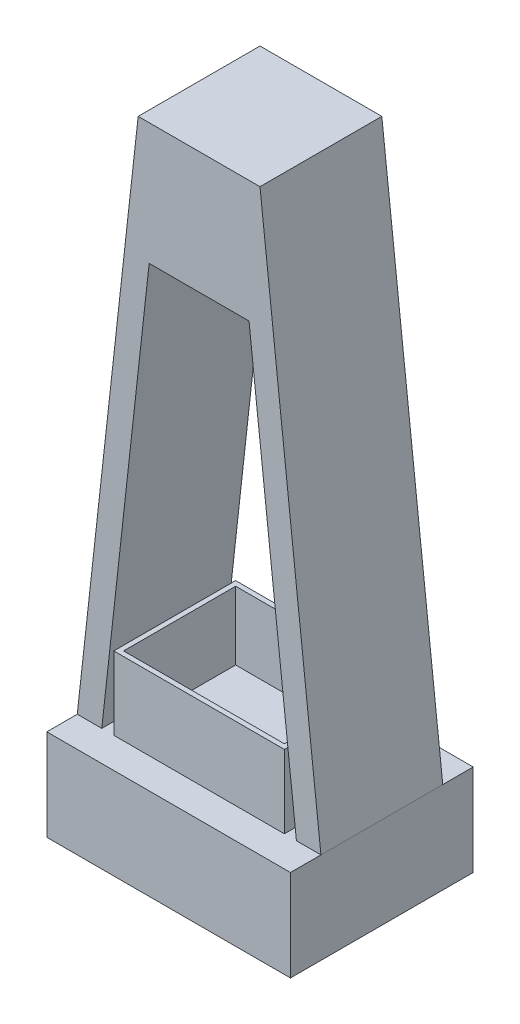
SolidWorks part; units mm, degrees
ref_plane "Front Plane" through (0, 0, 0) normal (0, 0, 1) x (1, 0, 0)
ref_plane "Top Plane" through (0, 0, 0) normal (0, 1, 0) x (1, 0, 0)
ref_plane "Right Plane" through (0, 0, 0) normal (1, 0, 0) x (0, 0, -1)
sketch "Sketch2" plane through (0, 0, 0) normal (0, 0, 1) x (1, 0, 0)
  line L0 (-50, 225) -> (50, 225)
  line L1 (50, 225) -> (100, -225)
  line L2 (100, -225) -> (-100, -225)
  line L3 (-100, -225) -> (-50, 225)
  point P3 (-48.9615, 146.9013)
  point P5 (0, 225)
  point P6 (0, -225)
  point P7 (-64.057, 145.9255)
  point P8 (-75, 0)
  dimension "D1" = 450
  dimension "D2" = 200
  dimension "D3" = 100
extrude "Boss-Extrude1" add sketch "Sketch2" along normal blind 100
sketch "Sketch3" plane through (0, -225, 0) normal (0, -1, 0) x (1, 0, 0)
  line L0 (-100, 100) -> (-100, 0) construction
  line L1 (-100, -25) -> (100, -25)
  line L2 (-100, -25) -> (-100, 125)
  line L3 (-100, 125) -> (100, 125)
  line L4 (100, -25) -> (100, 125)
  line L5 (-100, -25) -> (100, 125) construction
  line L6 (-100, 125) -> (100, -25) construction
  line L7 (-100, 0) -> (100, 0) construction
  point P0 (0, 50)
  point P7 (-100, 50)
  point P8 (0, 0)
  point P11 (0, 0)
  dimension "D1" = 150
extrude "Boss-Extrude2" add sketch "Sketch3" along normal blind 75
sketch "Sketch5" plane through (0, 0, 0) normal (0, 0, -1) x (-1, 0, 0)
  line L0 (-40.988, 125) -> (40.988, 125)
  line L1 (40.988, 125) -> (79.8769, -225)
  line L2 (79.8769, -225) -> (-79.8769, -225)
  line L3 (-79.8769, -225) -> (-40.988, 125)
  line L4 (50, 225) -> (100, -225) construction
  line L5 (-100, -225) -> (-50, 225) construction
  line L6 (-50, 225) -> (50, 225) construction
  line L7 (100, -225) -> (-100, -225) construction
  dimension "D1" = 100
  dimension "D2" = 20
  dimension "D3" = 20
extrude "Cut-Extrude2" cut sketch "Sketch5" against normal through all
sketch "Sketch6" plane through (0, 0, 0) normal (0, 0, -1) x (-1, 0, 0)
  line L0 (100, -225) -> (-100, -225) construction
  line L1 (-70, -225) -> (70, -225)
  line L2 (-70, -225) -> (-70, -165)
  line L3 (-70, -165) -> (70, -165)
  line L4 (70, -225) -> (70, -165)
  line L5 (-79.8769, -225) -> (-100, -225) construction
  point P6 (0, -165)
  point P10 (0, 0)
  point P11 (-68.514, -140)
  dimension "D1" = 60
  dimension "D2" = 140
extrude "Boss-Extrude3" add sketch "Sketch6" against normal up to surface (100 mm away) up to face at (0, -25, 100)
sketch "Sketch7" plane through (0, -165, 0) normal (0, 1, 0) x (1, 0, 0)
  line L0 (70, -100) -> (70, 0) construction
  line L1 (-66, -96) -> (66, -96)
  line L2 (-66, -96) -> (-66, -4)
  line L3 (-66, -4) -> (66, -4)
  line L4 (66, -96) -> (66, -4)
  line L5 (-66, -96) -> (66, -4) construction
  line L6 (-66, -4) -> (66, -96) construction
  line L7 (70, -100) -> (-70, -100) construction
  line L8 (-70, 0) -> (70, 0) construction
  point P0 (0, -50)
  point P9 (0, 0)
  point P12 (0, 0)
  point P13 (0, 0)
  point P14 (70, -50)
  dimension "D1" = 4
  dimension "D2" = 4
extrude "Cut-Extrude3" cut sketch "Sketch7" against normal offset from surface (56 mm away) 4 up to face at (0, -225, 50)
equation "\"D3@Sketch5\"=\"D2@Sketch5\""
